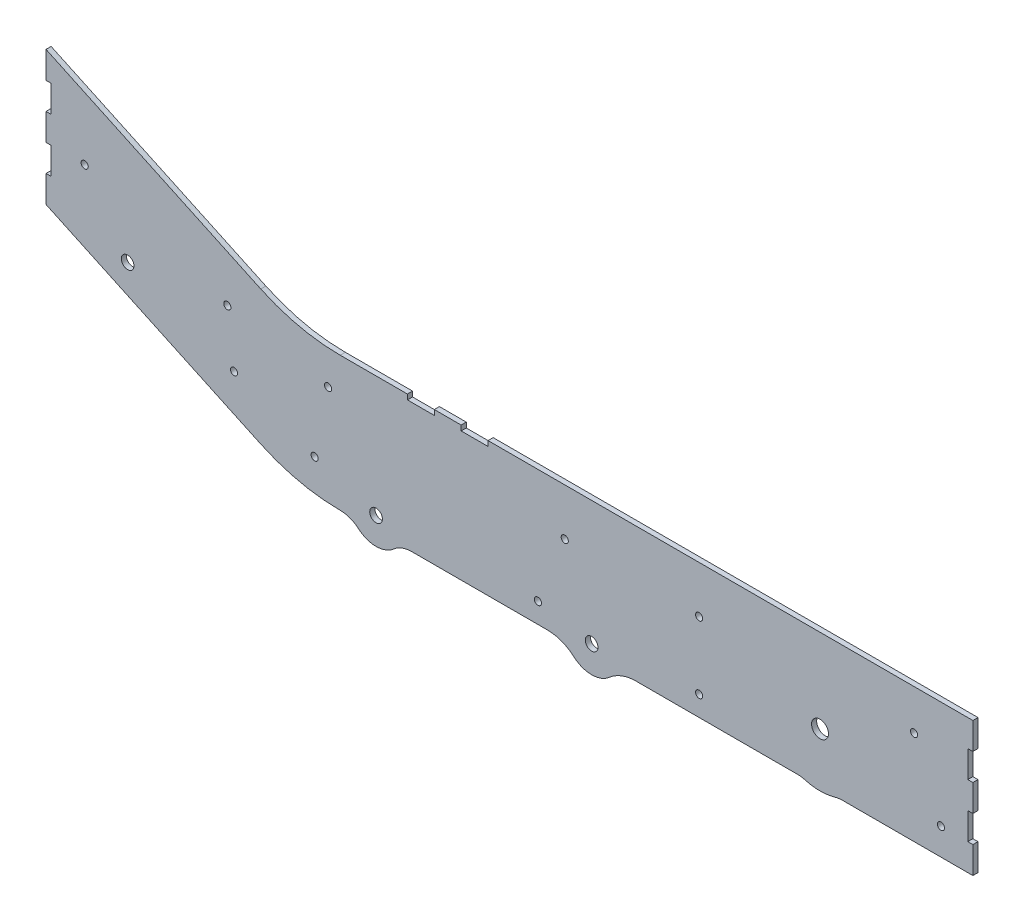
SolidWorks part; units mm, degrees
material "1060 Alloy"
ref_plane "Front Plane" through (0, 0, 0) normal (0, 0, 1) x (1, 0, 0)
ref_plane "Top Plane" through (0, 0, 0) normal (0, 1, 0) x (1, 0, 0)
ref_plane "Right Plane" through (0, 0, 0) normal (1, 0, 0) x (0, 0, -1)
sketch "standoff holes lower" plane through (0, 0, 0) normal (0, 0, 1) x (1, 0, 0)
  circle A7 centre (95.25, 85.725) radius 3.3782
  circle A8 centre (95.25, 12.7) radius 3.3782
  circle A9 centre (171.45, 12.7) radius 3.3782
  circle A10 centre (171.45, 85.725) radius 3.3782
  circle A12 centre (298.45, 12.7) radius 3.3782
  circle A13 centre (450.85, 85.725) radius 3.3782
  circle A16 centre (273.05, 85.725) radius 3.3782
  point P21 (0, 0)
sketch "axle holes lower" plane through (0, 0, 0) normal (0, 0, 1) x (1, 0, 0)
  line L10 (514.35, 98.425) -> (75.4368, 98.425) construction
  line L11 (66.0749, 94.3067) -> (3.3381, 25.8666) construction
  line L12 (0, 17.2849) -> (0, 12.7) construction
  line L13 (12.7, 0) -> (514.35, 0) construction
  line L14 (527.05, 12.7) -> (527.05, 85.725) construction
  circle A1 centre (247.65, 15.24) radius 4.826
  circle A4 centre (19.05, 19.05) radius 4.826
  arc A10 (527.05, 85.725) -> (514.35, 98.425) centre (514.35, 85.725) ccw construction
  arc A11 (75.4368, 98.425) -> (66.0749, 94.3067) centre (75.4368, 85.725) ccw construction
  arc A12 (3.3381, 25.8666) -> (0, 17.2849) centre (12.7, 17.2849) ccw construction
  arc A13 (0, 12.7) -> (12.7, 0) centre (12.7, 12.7) ccw construction
  arc A14 (514.35, 0) -> (527.05, 12.7) centre (514.35, 12.7) ccw construction
  circle A15 centre (476.25, 19.05) radius 4.826
sketch "lower box" plane through (0, 0, 0) normal (0, 0, 1) x (1, 0, 0)
  line L1 (622.3, 0) -> (-254, 0) construction
  line L2 (622.3, 0) -> (622.3, 25.4) construction
  line L3 (622.3, 127) -> (-254, 127) construction
  line L4 (-254, 0) -> (-254, 127) construction
  line L6 (527.05, 12.7) -> (527.05, 85.725) construction
  line L7 (622.3, 101.6) -> (622.3, 127) construction
  line L8 (622.3, 101.6) -> (617.474, 101.6) construction
  line L10 (622.3, 76.2) -> (617.474, 76.2) construction
  line L11 (617.474, 101.6) -> (617.474, 76.2) construction
  line L12 (622.3, 50.8) -> (617.474, 50.8) construction
  line L14 (622.3, 25.4) -> (617.474, 25.4) construction
  line L15 (617.474, 50.8) -> (617.474, 25.4) construction
  line L16 (622.3, 50.8) -> (622.3, 76.2) construction
  dimension "D1" = 127
  dimension "D2" = 876.3
  dimension "D3" = 95.25
  dimension "D4" = 4.826
sketch "alxe holes upper" plane through (0, 0, 0) normal (0, 0, 1) x (1, 0, 0)
  line L0 (-219.7848, 130.4205) -> (-230.5193, 107.4003) construction
  line L1 (-230.5193, 107.4003) -> (8.3155, -3.9702) construction
  line L3 (8.3155, -3.9702) -> (19.05, 19.05) construction
  line L4 (622.3, 0) -> (-254, 0) construction
  circle A0 centre (19.05, 19.05) radius 4.826 construction
  circle A2 centre (-219.7848, 130.4205) radius 4.826
  circle A3 centre (19.05, 19.05) radius 4.826
  dimension "D4" = 25
  dimension "D1" = 25.4
  dimension "D2" = 25.4
  dimension "D3" = 263.525
sketch "standoff holes upper" plane through (0, 0, 0) normal (0, 0, 1) x (1, 0, 0)
  line L0 (-162.9561, 84.3028) -> (-166.1764, 77.3967) construction
  line L1 (-226.6865, 105.613) -> (11.2395, -5.3337) construction
  line L4 (-37.2808, 64.9356) -> (-55.5295, 25.8012) construction
  line L5 (-230.5193, 107.4003) -> (8.3155, -3.9702) construction
  circle A2 centre (-162.9561, 84.3028) radius 3.3782
  circle A3 centre (-37.2808, 64.9356) radius 3.3782
  dimension "D2" = 7.62
  dimension "D1" = 43.18
sketch "upper shadow" plane through (0, 0, 0) normal (0, 0, 1) x (1, 0, 0)
  line L0 (-230.5193, 107.4003) -> (8.3155, -3.9702) construction
  line L4 (33.2535, 40.1076) -> (-204.2179, 150.8423) construction
  line L5 (-230.5193, 107.4003) -> (8.3155, -3.9702) construction
  arc A4 (8.3155, -3.9702) -> (33.2535, 40.1076) centre (19.05, 19.05) ccw construction
  arc A5 (-204.2179, 150.8423) -> (-230.5193, 107.4003) centre (-216.8161, 128.7868) ccw construction
  dimension "D1" = 25.4
  dimension "D2" = 25.4
sketch "upper box" plane through (0, 0, 0) normal (0, 0, 1) x (1, 0, 0)
  line L0 (-15.224, 0) -> (-254, 111.3431) construction
  line L1 (622.3, 0) -> (-254, 0) construction
  line L2 (-254, 111.3431) -> (-254, 136.7431) construction
  line L3 (-254, 238.3431) -> (257.1283, 0) construction
  line L4 (12.7, 0) -> (514.35, 0) construction
  line L5 (-254, 0) -> (-254, 127) construction
  line L6 (-230.5193, 107.4003) -> (8.3155, -3.9702) construction
  line L7 (-254, 212.9431) -> (-254, 238.3431) construction
  line L8 (-254, 212.9431) -> (-249.174, 212.9431) construction
  line L9 (-254, 162.1431) -> (-254, 187.5431) construction
  line L10 (-254, 187.5431) -> (-249.174, 187.5431) construction
  line L11 (-249.174, 212.9431) -> (-249.174, 187.5431) construction
  line L12 (-254, 162.1431) -> (-249.174, 162.1431) construction
  line L14 (-254, 136.7431) -> (-249.174, 136.7431) construction
  line L15 (-249.174, 162.1431) -> (-249.174, 136.7431) construction
  dimension "D1" = 127
  dimension "D2" = 6.35
  dimension "D3" = 4.826
sketch "outer face" plane through (0, 0, 0) normal (0, 0, 1) x (1, 0, 0)
  line L0 (622.3, 0) -> (-254, 0) construction
  line L1 (622.3, 0) -> (622.3, 25.4) construction
  line L2 (622.3, 25.4) -> (617.474, 25.4) construction
  line L3 (617.474, 50.8) -> (617.474, 25.4) construction
  line L4 (622.3, 50.8) -> (617.474, 50.8) construction
  line L5 (622.3, 50.8) -> (622.3, 76.2) construction
  line L6 (622.3, 76.2) -> (617.474, 76.2) construction
  line L7 (617.474, 101.6) -> (617.474, 76.2) construction
  line L8 (622.3, 101.6) -> (622.3, 127) construction
  line L9 (622.3, 101.6) -> (617.474, 101.6) construction
  line L10 (622.3, 127) -> (-254, 127) construction
  line L11 (-254, 238.3431) -> (257.1283, 0) construction
  line L12 (-254, 212.9431) -> (-254, 238.3431) construction
  line L13 (-254, 212.9431) -> (-249.174, 212.9431) construction
  line L14 (-249.174, 212.9431) -> (-249.174, 187.5431) construction
  line L15 (-249.174, 162.1431) -> (-249.174, 136.7431) construction
  line L16 (-254, 136.7431) -> (-249.174, 136.7431) construction
  line L17 (-254, 111.3431) -> (-254, 136.7431) construction
  line L18 (-15.224, 0) -> (-254, 111.3431) construction
  line L19 (-254, 162.1431) -> (-249.174, 162.1431) construction
  line L20 (-254, 162.1431) -> (-254, 187.5431) construction
  line L21 (-254, 187.5431) -> (-249.174, 187.5431) construction
  line L22 (622.3, 0) -> (24.1933, 0)
  line L23 (622.3, 0) -> (622.3, 25.4)
  line L24 (622.3, 25.4) -> (617.474, 25.4)
  line L25 (617.474, 50.8) -> (617.474, 25.4)
  line L26 (622.3, 50.8) -> (617.474, 50.8)
  line L27 (622.3, 50.8) -> (622.3, 76.2)
  line L28 (622.3, 76.2) -> (617.474, 76.2)
  line L29 (617.474, 101.6) -> (617.474, 76.2)
  line L30 (622.3, 101.6) -> (622.3, 127)
  line L31 (622.3, 101.6) -> (617.474, 101.6)
  line L32 (622.3, 127) -> (24.1933, 127)
  line L33 (-254, 238.3431) -> (-50.9483, 143.6585)
  line L34 (-254, 212.9431) -> (-254, 238.3431)
  line L35 (-254, 212.9431) -> (-249.174, 212.9431)
  line L36 (-249.174, 212.9431) -> (-249.174, 187.5431)
  line L37 (-249.174, 162.1431) -> (-249.174, 136.7431)
  line L38 (-254, 136.7431) -> (-249.174, 136.7431)
  line L39 (-254, 111.3431) -> (-254, 136.7431)
  line L40 (-50.9483, 16.6585) -> (-254, 111.3431)
  line L41 (-254, 162.1431) -> (-249.174, 162.1431)
  line L42 (-254, 162.1431) -> (-254, 187.5431)
  line L43 (-254, 187.5431) -> (-249.174, 187.5431)
  arc A0 (-50.9483, 16.6585) -> (24.1933, 0) centre (24.1933, 177.8) ccw
  arc A1 (24.1933, 127) -> (-50.9483, 143.6585) centre (24.1933, 304.8) cw
  dimension "D1" = 177.8
extrude "Boss-Extrude1" add sketch "outer face" along normal blind 4.826
sketch "Sketch5" plane through (0, 0, 4.826) normal (0, 0, 1) x (1, 0, 0)
  line L1 (-249.174, 162.1431) -> (-249.174, 136.7431) construction
  line L2 (622.3, 127) -> (24.1933, 127) construction
  line L4 (617.474, 76.2) -> (617.474, 101.6) construction
  line L5 (622.3, 127) -> (24.1933, 127) construction
  line L6 (414.2486, 5.4392) -> (414.2486, 130.8517) construction
  line L7 (24.1933, 0) -> (622.3, 0) construction
  line L8 (617.474, 25.4) -> (617.474, 50.8) construction
  circle A9 centre (-76.2, 63.5) radius 3.3782
  circle A10 centre (-82.55, 114.3) radius 3.3782
  circle A11 centre (592.074, 25.4) radius 3.3782
  circle A12 centre (0, 31.75) radius 3.3782
  circle A13 centre (211.0486, 19.05) radius 3.3782
  circle A14 centre (236.4486, 82.55) radius 3.3782
  circle A15 centre (363.4486, 82.55) radius 3.3782
  circle A16 centre (363.4486, 19.05) radius 3.3782
  circle A17 centre (566.674, 88.9) radius 3.3782
  circle A18 centre (12.7, 95.25) radius 3.3782
  circle A19 centre (-217.424, 162.1431) radius 3.3782
  dimension "D9" = 127
  dimension "D10" = 152.4
  dimension "D11" = 19.05
  dimension "D12" = 44.45
  dimension "D13" = 6.7564
  dimension "D7" = 19.05
  dimension "D14" = 25.4
  dimension "D15" = 25.4
  dimension "D17" = 31.75
  dimension "D16" = 82.55
  dimension "D18" = 82.55
  dimension "D19" = 76.2
  dimension "D20" = 31.75
  dimension "D21" = 31.75
  dimension "D22" = 50.8
  dimension "D23" = 63.5
  dimension "D24" = 12.7
  dimension "D3" = 38.1
  dimension "D4" = 50.8
  dimension "D5" = 44.45
  dimension "D6" = 50.8
  dimension "D8" = 50.8
extrude "standoff hole" cut sketch "Sketch5" against normal through all
sketch "Sketch6" plane through (0, 0, 4.826) normal (0, 0, 1) x (1, 0, 0)
  circle A0 centre (-219.7848, 130.4205) radius 4.826 construction
  circle A1 centre (19.05, 19.05) radius 4.826 construction
  circle A2 centre (247.65, 15.24) radius 4.826 construction
  circle A4 centre (-219.7848, 130.4205) radius 4.826
  circle A5 centre (19.05, 19.05) radius 4.826 construction
  circle A6 centre (247.65, 15.24) radius 4.826 construction
extrude "axle holes" [suppressed] cut sketch "Sketch6" against normal through all
sketch "Sketch7" plane through (0, 0, 4.826) normal (0, 0, 1) x (1, 0, 0)
  line L0 (-231.2949, 135.7877) -> (-196.7645, 119.686) construction
  line L1 (-229.2553, 140.1616) -> (-194.725, 124.0598)
  line L2 (-233.3344, 131.4139) -> (-198.8041, 115.3121)
  line L3 (-230.5193, 107.4003) -> (8.3155, -3.9702) construction
  circle A0 centre (-219.7848, 130.4205) radius 4.826 construction
  circle A1 centre (-219.7848, 130.4205) radius 4.826
  arc A2 (-229.2553, 140.1616) -> (-233.3344, 131.4139) centre (-231.2949, 135.7877) ccw
  arc A3 (-198.8041, 115.3121) -> (-194.725, 124.0598) centre (-196.7645, 119.686) ccw
  point P5 (-214.0297, 127.7369)
  dimension "D1" = 38.1
  dimension "D2" = 12.7
extrude "front slot" [suppressed] cut sketch "Sketch7" against normal through all
sketch "Sketch8" plane through (0, 0, 4.826) normal (0, 0, 1) x (1, 0, 0)
  line L0 (113.0933, 127) -> (113.0933, 122.174) construction
  line L1 (87.6933, 122.174) -> (113.0933, 122.174)
  line L2 (87.6933, 122.174) -> (87.6933, 127)
  line L3 (87.6933, 127) -> (113.0933, 127)
  line L4 (113.0933, 122.174) -> (113.0933, 127)
  line L5 (622.3, 127) -> (24.1933, 127) construction
  line L6 (113.0933, 122.174) -> (138.4933, 122.174) construction
  line L7 (138.4933, 122.174) -> (163.8933, 122.174)
  line L8 (138.4933, 122.174) -> (138.4933, 127)
  line L9 (138.4933, 127) -> (163.8933, 127)
  line L10 (163.8933, 122.174) -> (163.8933, 127)
  line L11 (62.2933, 122.174) -> (189.2933, 122.174)
  line L12 (62.2933, 122.174) -> (62.2933, 127)
  line L13 (62.2933, 127) -> (189.2933, 127)
  line L14 (189.2933, 122.174) -> (189.2933, 127)
  line L15 (163.8933, 127) -> (163.8933, 122.174) construction
  point P18 (125.7933, 122.174)
  point P19 (125.7933, 122.174)
  line M29 (622.3, 127) -> (24.1933, 127)
  dimension "D1" = 127
extrude "top slots" cut sketch "Sketch8" against normal through all contours L1 L4 L2 M29 | L7 L10 L8 M29
sketch "Sketch9" plane through (0, 0, 4.826) normal (0, 0, 1) x (1, 0, 0)
  line L0 (365.4629, -63.5) -> (553.974, -63.5) construction
  line L1 (24.1933, 0) -> (622.3, 0) construction
  line L2 (-108.841, -24.5) -> (199.7287, -24.5) construction
  line L3 (553.974, -63.5) -> (553.974, 63.787) construction
  line L4 (617.474, 25.4) -> (617.474, 50.8) construction
  line L5 (24.1933, 0) -> (622.3, 0)
  circle A0 centre (477.774, 47.8) radius 76.2 construction
  circle A1 centre (477.774, 47.8) radius 8
  arc A2 (463.6602, -1) -> (491.8878, -1) centre (477.774, 47.8) ccw
  arc A3 (498.9447, 0) -> (491.8878, -1) centre (498.9447, -25.4) ccw
  arc A4 (463.6602, -1) -> (456.6033, 0) centre (456.6033, -25.4) ccw
  dimension "D1" = 152.4
  dimension "D4" = 16
  dimension "D5" = 50.8
  dimension "D6" = 25.4
  dimension "D7" = 25.4
  dimension "D2" = 63.5
  dimension "D3" = 63.5
extrude "back axle extension" add sketch "Sketch9" against normal up to surface (4.826 mm away) contours A4 A2 A3 L5 up to face at (-214.0458, 162.1431, 0)
sketch "Sketch11" plane through (0, 0, 4.826) normal (0, 0, 1) x (1, 0, 0)
  line L0 (24.1933, 0) -> (456.6033, 0) construction
  line L1 (24.1933, 0) -> (456.6033, 0)
  line L2 (561.7812, -27.675) -> (321.8375, -27.675) construction
  line L3 (219.9579, 0) -> (303.7901, 0)
  arc A0 (471.7538, 123.0345) -> (489.1691, 122.4098) centre (477.774, 47.8) ccw construction
  arc A1 (471.7538, 123.0345) -> (489.1691, 122.4098) centre (477.774, 47.8) ccw
  circle A2 centre (261.874, 9.6) radius 37.275 construction
  arc A5 (258.0857, 46.682) -> (275.1308, 44.438) centre (261.874, 9.6) ccw construction
  arc A6 (258.0857, 46.682) -> (275.1308, 44.438) centre (261.874, 9.6) ccw construction
  arc A7 (245.1076, -9.48) -> (278.6404, -9.48) centre (261.874, 9.6) ccw
  arc A8 (303.7901, 0) -> (278.6404, -9.48) centre (303.7901, -38.1) ccw
  arc A9 (245.1076, -9.48) -> (219.9579, 0) centre (219.9579, -38.1) ccw
  dimension "D1" = 215.9
  dimension "D2" = 25.4
  dimension "D3" = 38.1
extrude "lower small axle extension" add sketch "Sketch11" against normal up to surface (4.826 mm away) contours A9 A7 A8 L1 up to face at (-214.0458, 162.1431, 0)
sketch "Sketch13" plane through (0, 0, 4.826) normal (0, 0, 1) x (1, 0, 0)
  line L0 (247.3066, -27.675) -> (540.2367, -27.675) construction
  line L1 (-379.1984, 175.5439) -> (-126.1027, 57.5235) construction
  line L3 (24.1933, 0) -> (219.9579, 0) construction
  line L4 (24.1933, 0) -> (219.9579, 0)
  line L5 (34.8342, -24.5) -> (123.7671, -24.5) construction
  line L6 (-254, 111.3431) -> (-50.9483, 16.6585) construction
  arc A0 (471.7538, 123.0345) -> (489.1691, 122.4098) centre (477.774, 47.8) ccw construction
  arc A1 (258.0857, 46.682) -> (275.1308, 44.438) centre (261.874, 9.6) ccw construction
  arc A2 (471.7538, 123.0345) -> (489.1691, 122.4098) centre (477.774, 47.8) ccw construction
  arc A3 (258.0857, 46.682) -> (275.1308, 44.438) centre (261.874, 9.6) ccw construction
  circle A5 centre (58.0608, 12.775) radius 37.275 construction
  arc A7 (-216.5193, 150.4121) -> (-212.4402, 159.1598) centre (-214.4798, 154.786) ccw construction
  circle A8 centre (-214.4798, 154.786) radius 50.8 construction
  arc A9 (41.4343, -6.427) -> (74.6874, -6.427) centre (58.0608, 12.775) ccw
  arc A12 (245.1076, -9.48) -> (278.6404, -9.48) centre (261.874, 9.6) ccw construction
  arc A13 (91.9284, 0) -> (74.6874, -6.427) centre (91.9284, -26.3388) ccw
  arc A14 (41.4343, -6.427) -> (24.1933, 0) centre (24.1933, -26.3388) ccw
  dimension "D1" = 101.6
  dimension "D2" = 3.175
extrude "front small axle extension" add sketch "Sketch13" against normal up to surface (4.826 mm away) contours A14 A9 A13 L4 up to face at (-214.0458, 162.1431, 0)
sketch "Sketch14" plane through (0, 0, 4.826) normal (0, 0, 1) x (1, 0, 0)
  line L0 (-254, 111.3431) -> (-50.9483, 16.6585) construction
  line L1 (-254, 111.3431) -> (-50.9483, 16.6585)
  line L2 (-257.2377, 118.6727) -> (104.2967, -49.9135) construction
  line L3 (-217.2405, 100.0217) -> (-175.6892, 189.1288) construction
  arc A0 (54.2725, 49.857) -> (71.3176, 47.613) centre (58.0608, 12.775) ccw construction
  arc A1 (54.2725, 49.857) -> (71.3176, 47.613) centre (58.0608, 12.775) ccw
  circle A2 centre (-149.7311, 124.5932) radius 50.8 construction
  dimension "D1" = 101.6
  dimension "D2" = 38.1
sketch "Sketch10" plane through (0, 0, 4.826) normal (0, 0, 1) x (1, 0, 0)
  line L0 (-160.0111, 84.8653) -> (-160.0111, 57.6219) construction
  line L1 (-176.8431, 98.8307) -> (-176.8431, 65.4225) construction
  line L2 (-143.4345, 102.5476) -> (-187.906, 102.5476) construction
  circle A0 centre (477.774, 47.8) radius 8
  circle A1 centre (261.874, 9.6) radius 6
  circle A2 centre (58.0608, 12.775) radius 6
  circle A3 centre (-176.8431, 102.5476) radius 6
  dimension "D1" = 16
  dimension "D2" = 12
  dimension "D3" = 12
  dimension "D4" = 16.832
extrude "new axle holes" cut sketch "Sketch10" against normal through all
equation "\"w\"= .19"
equation "\"D4@lower box\" = \"w\""
equation "\"D3@upper box\"=\"w\""
equation "\"D1@Boss-Extrude1\"=\"w\""
